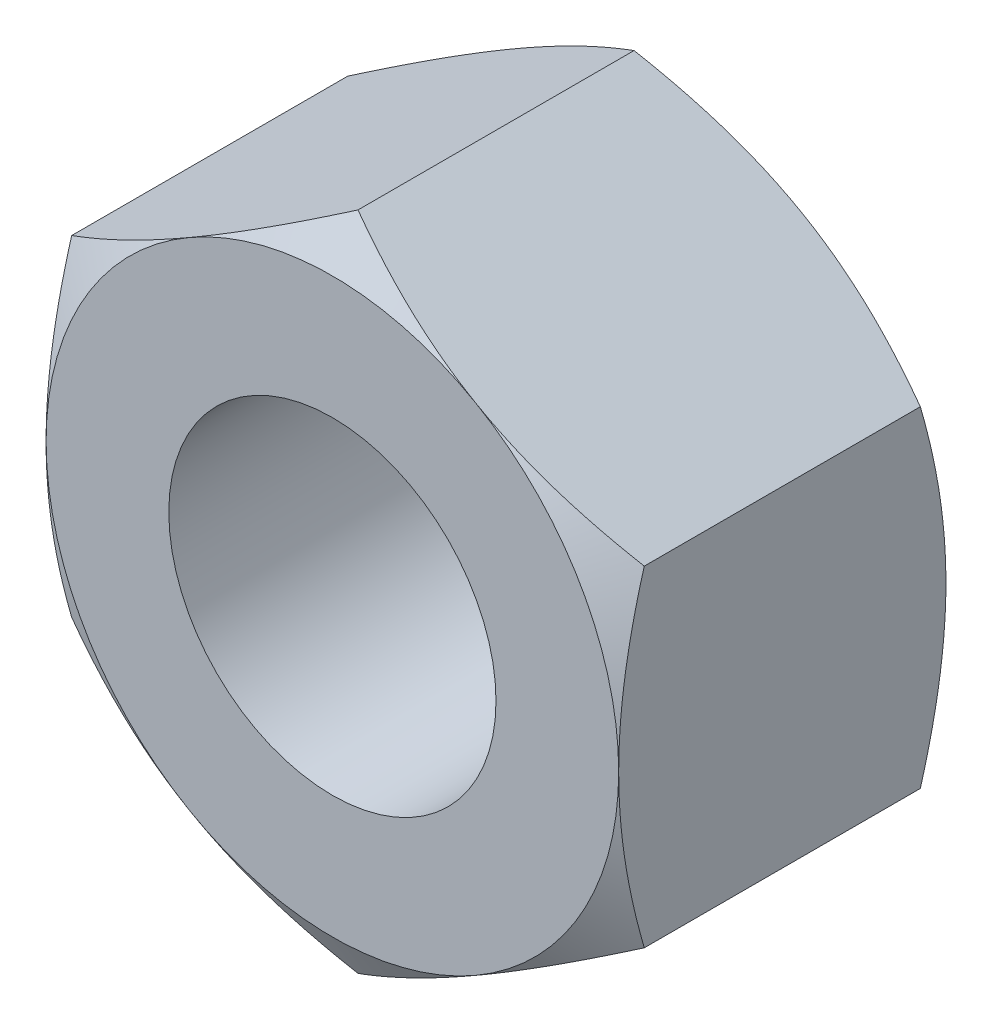
SolidWorks part; units mm, degrees
ref_plane "Plan de face" through (0, 0, 0) normal (0, 0, 1) x (1, 0, 0)
ref_plane "Plan de dessus" through (0, 0, 0) normal (0, 1, 0) x (1, 0, 0)
ref_plane "Plan de droite" through (0, 0, 0) normal (1, 0, 0) x (0, 0, -1)
sketch "Esquisse1" plane through (0, 0, 0) normal (0, 0, 1) x (1, 0, 0)
  line L1 (0, 4.0415) -> (-3.5, 2.0207)
  line L2 (-3.5, 2.0207) -> (-3.5, -2.0207)
  line L3 (-3.5, -2.0207) -> (0, -4.0415)
  line L4 (0, -4.0415) -> (3.5, -2.0207)
  line L5 (3.5, -2.0207) -> (3.5, 2.0207)
  line L6 (3.5, 2.0207) -> (0, 4.0415)
  circle A0 centre (0, 0) radius 3.5 construction
  dimension "D1" = 7
extrude "Boss.-Extru.1" add sketch "Esquisse1" along normal blind 4
sketch "Esquisse2" plane through (0, 0, 4) normal (0, 0, 1) x (1, 0, 0)
  circle A0 centre (0, 0) radius 2
  dimension "D1" = 4
extrude "Enlèv. mat.-Extru.1" cut sketch "Esquisse2" against normal up to next
sketch "Esquisse4" plane through (0, 0, 0) normal (0, 1, 0) x (1, 0, 0)
  line L0 (-6.9641, -2) -> (-1.7679, 1)
  line L1 (0, 0) -> (-3.5, 0) construction
  line L3 (-6.9641, -2) -> (-1.7679, -5)
  line L4 (-1.7679, 1) -> (-7.9641, 1)
  line L5 (-7.9641, 1) -> (-7.9641, -5)
  line L6 (-7.9641, -5) -> (-1.7679, -5)
  line L7 (0, 0) -> (0, -4) construction
  dimension "D1" = 1
  dimension "D2" = 1
  dimension "D3" = 30
revolve "Enlèvement de matière-Révolution8" cut sketch "Esquisse4" angle 360 about L7
